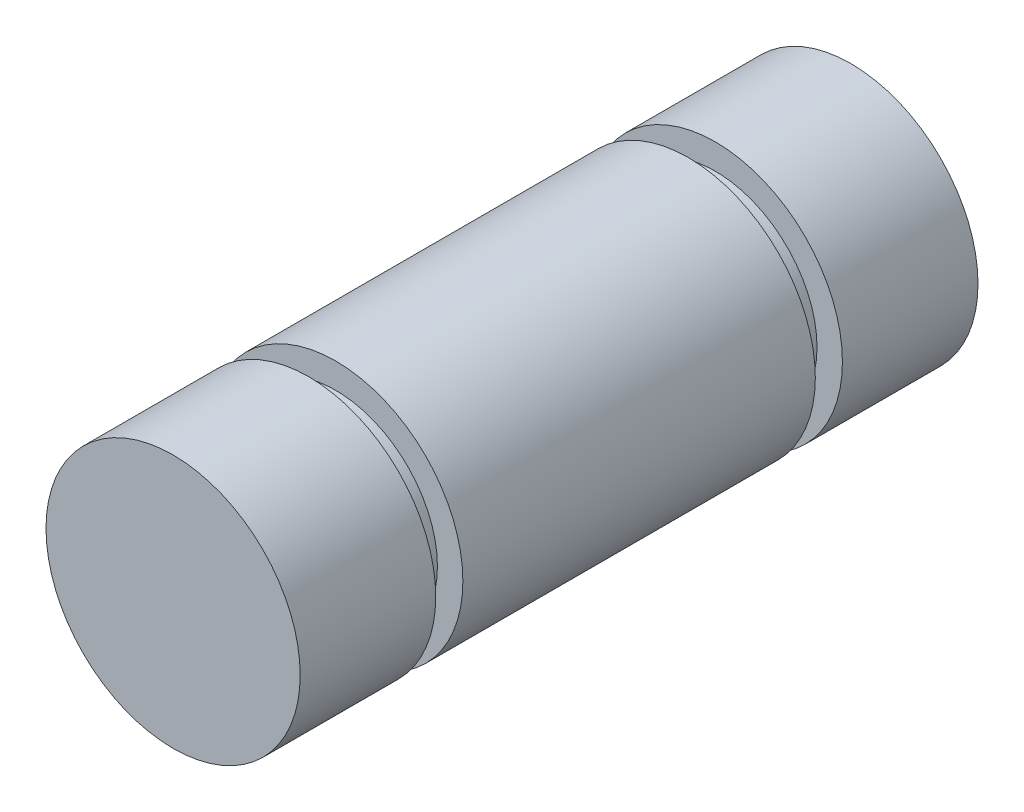
SolidWorks part; units mm, degrees
ref_plane "Front Plane" through (0, 0, 0) normal (0, 0, 1) x (1, 0, 0)
ref_plane "Top Plane" through (0, 0, 0) normal (0, 1, 0) x (1, 0, 0)
ref_plane "Right Plane" through (0, 0, 0) normal (1, 0, 0) x (0, 0, -1)
sketch "Sketch1" plane through (0, 0, 0) normal (0, 0, 1) x (1, 0, 0)
  circle A0 centre (0, 0) radius 4.7625
  dimension "D1" = 9.525
extrude "Boss-Extrude1" add sketch "Sketch1" along normal mid plane 25.4
sketch "Sketch2" plane through (0, 0, 0) normal (0, 1, 0) x (1, 0, 0)
  line L0 (4.7625, -12.7) -> (4.7625, 12.7) construction
  line L1 (4.7625, 7.62) -> (3.81, 7.62)
  line L2 (4.7625, 7.62) -> (4.7625, 6.604)
  line L3 (4.7625, 6.604) -> (3.81, 6.604)
  line L4 (3.81, 7.62) -> (3.81, 6.604)
  line L5 (4.7625, 12.7) -> (-4.7625, 12.7) construction
  line L6 (4.7625, -6.604) -> (3.81, -6.604)
  line L7 (4.7625, -6.604) -> (4.7625, -7.62)
  line L8 (4.7625, -7.62) -> (3.81, -7.62)
  line L9 (3.81, -6.604) -> (3.81, -7.62)
  line L10 (-4.7625, -12.7) -> (4.7625, -12.7) construction
  point P10 (3.81, 7.112)
  dimension "D1" = 0.9525
  dimension "D2" = 0.9525
  dimension "D3" = 1.016
  dimension "D4" = 1.016
  dimension "D5" = 5.08
  dimension "D6" = 5.08
ref_axis "Axis1" through (0, 0, 12.7) along (0, 0, -1)
revolve "Cut-Revolve1" cut sketch "Sketch2" angle 360 about axis through (0, 0, 12.7) along (0, 0, -1)
